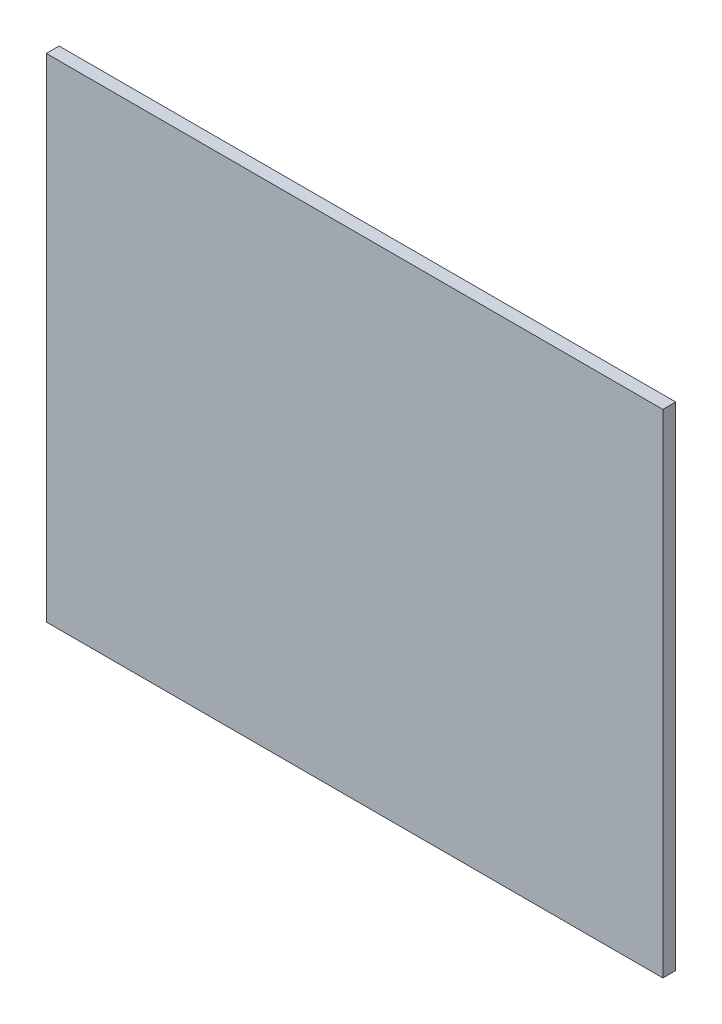
SolidWorks part; units mm, degrees
ref_plane "Front Plane" through (0, 0, 0) normal (0, 0, 1) x (1, 0, 0)
ref_plane "Top Plane" through (0, 0, 0) normal (0, 1, 0) x (1, 0, 0)
ref_plane "Right Plane" through (0, 0, 0) normal (1, 0, 0) x (0, 0, -1)
sketch "Sketch1" plane through (0, 0, 0) normal (0, 0, 1) x (1, 0, 0)
  line L1 (0, 0) -> (288, 0)
  line L2 (0, 0) -> (0, 230)
  line L3 (0, 230) -> (288, 230)
  line L4 (288, 0) -> (288, 230)
  dimension "D1" = 230
  dimension "D2" = 288
extrude "Boss-Extrude1" add sketch "Sketch1" along normal blind 6
